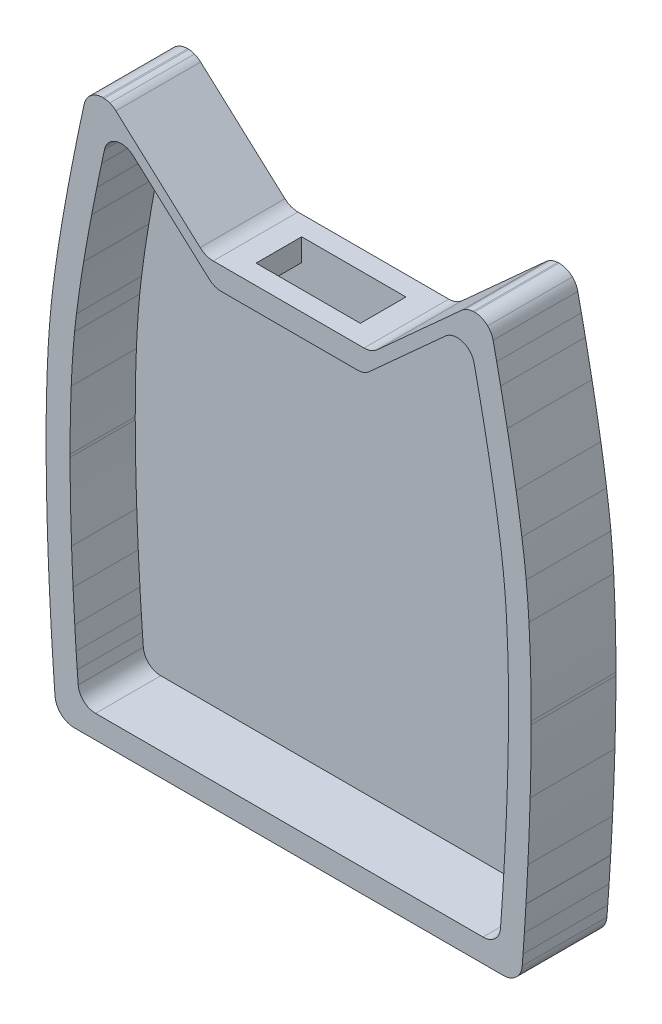
SolidWorks part; units mm, degrees
ref_plane "Front Plane" through (0, 0, 0) normal (0, 0, 1) x (1, 0, 0)
ref_plane "Top Plane" through (0, 0, 0) normal (0, 1, 0) x (1, 0, 0)
ref_plane "Right Plane" through (0, 0, 0) normal (1, 0, 0) x (0, 0, -1)
sketch "Sketch1" plane through (0, 0, 0) normal (0, 0, 1) x (1, 0, 0)
  line L0 (-74610.4504, -128792.8101) -> (-74623.3809, -128804.5097)
  line L1 (-74625.3861, -128805.2822) -> (-74648.5276, -128805.2822)
  line L2 (-74650.5328, -128804.5097) -> (-74663.4632, -128792.8101)
  line L3 (-74669.8394, -128877.9744) -> (-74604.0742, -128877.9744)
  arc A0 (-74625.3861, -128805.2822) -> (-74623.3809, -128804.5097) centre (-74625.3861, -128802.2936) ccw
  arc A1 (-74650.5328, -128804.5097) -> (-74648.5276, -128805.2822) centre (-74648.5276, -128802.2936) ccw
  arc A2 (-74663.4632, -128792.8101) -> (-74664.4011, -128792.2295) centre (-74665.4871, -128795.0316) ccw
  arc A3 (-74664.4011, -128792.2295) -> (-74665.2428, -128792.0421) centre (-74665.4489, -128794.9516) ccw
  arc A4 (-74665.2428, -128792.0421) -> (-74665.4521, -128792.0346) centre (-74665.452, -128794.9829) ccw
  arc A5 (-74665.4521, -128792.0346) -> (-74668.1554, -128793.8043) centre (-74665.4666, -128794.9621) ccw
  arc A6 (-74668.1554, -128793.8043) -> (-74668.3285, -128794.3514) centre (-74665.3558, -128794.991) ccw
  arc A7 (-74668.3285, -128794.3514) -> (-74668.8127, -128796.6154) centre (-74210.4972, -128893.4524) ccw
  arc A8 (-74668.8127, -128796.6154) -> (-74669.6285, -128800.5607) centre (-74215.6319, -128892.3844) ccw
  arc A9 (-74669.6285, -128800.5607) -> (-74670.5013, -128804.9966) centre (-74256.6242, -128884.1197) ccw
  arc A10 (-74670.5013, -128804.9966) -> (-74671.8625, -128812.5722) centre (-74344.668, -128867.4549) ccw
  arc A11 (-74671.8625, -128812.5722) -> (-74673.0862, -128820.8532) centre (-74471.6696, -128846.3871) ccw
  arc A12 (-74673.0862, -128820.8532) -> (-74673.4036, -128823.655) centre (-74549.975, -128836.2185) ccw
  arc A13 (-74673.4036, -128823.655) -> (-74673.9737, -128831.9341) centre (-74531.0189, -128837.6186) ccw
  arc A14 (-74673.9737, -128831.9341) -> (-74674.1705, -128842.0393) centre (-74433.1903, -128841.6785) ccw
  arc A15 (-74674.1705, -128842.0393) -> (-74674.1702, -128842.5188) centre (-74370.5267, -128842.0386) ccw
  arc A16 (-74674.1702, -128842.5188) -> (-74673.9133, -128855.4252) centre (-74296.3228, -128841.454) ccw
  arc A17 (-74673.9133, -128855.4252) -> (-74673.6609, -128861.373) centre (-74198.726, -128838.2406) ccw
  arc A18 (-74673.6609, -128861.373) -> (-74673.3731, -128866.7142) centre (-74161.6475, -128836.4629) ccw
  arc A19 (-74673.3731, -128866.7142) -> (-74673.1367, -128870.4811) centre (-74157.7529, -128836.253) ccw
  arc A20 (-74673.1367, -128870.4811) -> (-74672.9536, -128873.1301) centre (-74183.7854, -128837.9879) ccw
  arc A21 (-74672.9536, -128873.1301) -> (-74672.795, -128875.2658) centre (-74236.2197, -128841.7641) ccw
  arc A22 (-74672.795, -128875.2658) -> (-74669.8394, -128877.9744) centre (-74669.8639, -128875.0343) ccw
  arc A23 (-74604.0742, -128877.9744) -> (-74601.1186, -128875.2658) centre (-74604.0497, -128875.0343) ccw
  arc A24 (-74601.1186, -128875.2658) -> (-74600.9941, -128873.6003) centre (-75030.7638, -128842.2862) ccw
  arc A25 (-74600.9941, -128873.6003) -> (-74600.7912, -128870.6962) centre (-75084.5949, -128838.3701) ccw
  arc A26 (-74600.7912, -128870.6962) -> (-74600.5445, -128866.7814) centre (-75115.5828, -128836.2889) ccw
  arc A27 (-74600.5445, -128866.7814) -> (-74600.5406, -128866.7142) centre (-75116.7394, -128836.2135) ccw
  arc A28 (-74600.5406, -128866.7142) -> (-74600.2528, -128861.3729) centre (-75112.2699, -128836.4627) ccw
  arc A29 (-74600.2528, -128861.3729) -> (-74599.8985, -128852.287) centre (-75060.7265, -128838.8707) ccw
  arc A30 (-74599.8985, -128852.287) -> (-74599.7435, -128842.5188) centre (-74960.805, -128841.6735) ccw
  arc A31 (-74599.7435, -128842.5188) -> (-74599.7431, -128842.0393) centre (-74903.4023, -128842.0386) ccw
  arc A32 (-74599.7431, -128842.0393) -> (-74600.0837, -128829.0796) centre (-74823.121, -128841.4254) ccw
  arc A33 (-74600.0837, -128829.0796) -> (-74600.51, -128823.655) centre (-74730.0928, -128836.5682) ccw
  arc A34 (-74600.51, -128823.655) -> (-74601.1701, -128818.2711) centre (-74740.6628, -128838.1057) ccw
  arc A35 (-74601.1701, -128818.2711) -> (-74602.0512, -128812.5722) centre (-74824.1765, -128849.8308) ccw
  arc A36 (-74602.0512, -128812.5722) -> (-74603.4124, -128804.9967) centre (-74929.2472, -128867.4551) ccw
  arc A37 (-74603.4124, -128804.9967) -> (-74604.4266, -128799.864) centre (-75021.4303, -128884.9284) ccw
  arc A38 (-74604.4266, -128799.864) -> (-74605.0365, -128796.9208) centre (-75059.738, -128892.69) ccw
  arc A39 (-74605.0365, -128796.9208) -> (-74605.5852, -128794.3514) centre (-75063.9174, -128893.5596) ccw
  arc A40 (-74605.5852, -128794.3514) -> (-74606.4193, -128792.8477) centre (-74608.4315, -128794.9471) ccw
  arc A41 (-74606.4193, -128792.8477) -> (-74608.4615, -128792.0346) centre (-74608.4597, -128795.0013) ccw
  arc A42 (-74608.4615, -128792.0346) -> (-74608.6709, -128792.0421) centre (-74608.4616, -128794.9829) ccw
  arc A43 (-74608.6709, -128792.0421) -> (-74610.011, -128792.478) centre (-74608.464, -128794.9556) ccw
  arc A44 (-74610.011, -128792.478) -> (-74610.4504, -128792.8101) centre (-74608.3795, -128795.0941) ccw
  dimension "D1" = 72.6922
extrude "Boss-Extrude1" add sketch "Sketch1" along normal blind 13
sketch "Sketch2" plane through (0, 0, 13) normal (0, 0, 1) x (1, 0, 0)
  line B0 (-74612.8969, -128797.442) -> (-74624.5846, -128808.0172)
  line B1 (-74626.397, -128808.7154) -> (-74647.3143, -128808.7154)
  line B2 (-74649.1268, -128808.0172) -> (-74660.8144, -128797.442)
  line B3 (-74666.5778, -128874.4209) -> (-74607.1335, -128874.4209)
  arc B4 (-74626.397, -128808.7154) -> (-74624.5846, -128808.0172) centre (-74626.397, -128806.0141) ccw
  arc B5 (-74649.1268, -128808.0172) -> (-74647.3143, -128808.7154) centre (-74647.3143, -128806.014) ccw
  arc B6 (-74660.8144, -128797.442) -> (-74661.6621, -128796.9173) centre (-74662.6437, -128799.45) ccw
  arc B7 (-74661.6621, -128796.9173) -> (-74662.423, -128796.7479) centre (-74662.6092, -128799.3777) ccw
  arc B8 (-74662.423, -128796.7479) -> (-74662.6122, -128796.7411) centre (-74662.6121, -128799.406) ccw
  arc B9 (-74662.6122, -128796.7411) -> (-74665.0556, -128798.3408) centre (-74662.6252, -128799.3872) ccw
  arc B10 (-74665.0556, -128798.3408) -> (-74665.2121, -128798.8352) centre (-74662.5251, -128799.4134) ccw
  arc B11 (-74665.2121, -128798.8352) -> (-74665.6497, -128800.8816) centre (-74251.3845, -128888.4113) ccw
  arc B12 (-74665.6497, -128800.8816) -> (-74666.3872, -128804.4478) centre (-74256.0257, -128887.446) ccw
  arc B13 (-74666.3872, -128804.4478) -> (-74667.176, -128808.4573) centre (-74293.0781, -128879.9756) ccw
  arc B14 (-74667.176, -128808.4573) -> (-74668.4064, -128815.3047) centre (-74372.6597, -128864.9125) ccw
  arc B15 (-74668.4064, -128815.3047) -> (-74669.5125, -128822.7899) centre (-74487.4547, -128845.8696) ccw
  arc B16 (-74669.5125, -128822.7899) -> (-74669.7994, -128825.3223) centre (-74558.234, -128836.6783) ccw
  arc B17 (-74669.7994, -128825.3223) -> (-74670.3147, -128832.8057) centre (-74541.0998, -128837.9439) ccw
  arc B18 (-74670.3147, -128832.8057) -> (-74670.4926, -128841.9397) centre (-74452.6738, -128841.6136) ccw
  arc B19 (-74670.4926, -128841.9397) -> (-74670.4923, -128842.3731) centre (-74396.033, -128841.9391) ccw
  arc B20 (-74670.4923, -128842.3731) -> (-74670.2601, -128854.039) centre (-74328.9611, -128841.4106) ccw
  arc B21 (-74670.2601, -128854.039) -> (-74670.032, -128859.4151) centre (-74240.7447, -128838.5061) ccw
  arc B22 (-74670.032, -128859.4151) -> (-74669.7718, -128864.243) centre (-74207.2299, -128836.8993) ccw
  arc B23 (-74669.7718, -128864.243) -> (-74669.5582, -128867.6479) centre (-74203.7096, -128836.7095) ccw
  arc B24 (-74669.5582, -128867.6479) -> (-74669.3927, -128870.0422) centre (-74227.2401, -128838.2777) ccw
  arc B25 (-74669.3927, -128870.0422) -> (-74669.2493, -128871.9726) centre (-74274.6347, -128841.691) ccw
  arc B26 (-74669.2493, -128871.9726) -> (-74666.5778, -128874.4209) centre (-74666.5999, -128871.7634) ccw
  arc B27 (-74607.1335, -128874.4209) -> (-74604.462, -128871.9726) centre (-74607.1114, -128871.7634) ccw
  arc B28 (-74604.462, -128871.9726) -> (-74604.3494, -128870.4673) centre (-74992.8125, -128842.1629) ccw
  arc B29 (-74604.3494, -128870.4673) -> (-74604.1661, -128867.8423) centre (-75041.4697, -128838.6231) ccw
  arc B30 (-74604.1661, -128867.8423) -> (-74603.9431, -128864.3037) centre (-75069.4793, -128836.7419) ccw
  arc B31 (-74603.9431, -128864.3037) -> (-74603.9395, -128864.243) centre (-75070.5247, -128836.674) ccw
  arc B32 (-74603.9395, -128864.243) -> (-74603.6793, -128859.4151) centre (-75066.4848, -128836.8991) ccw
  arc B33 (-74603.6793, -128859.4151) -> (-74603.3592, -128851.2025) centre (-75019.8954, -128839.0756) ccw
  arc B34 (-74603.3592, -128851.2025) -> (-74603.219, -128842.3731) centre (-74929.5777, -128841.609) ccw
  arc B35 (-74603.219, -128842.3731) -> (-74603.2187, -128841.9397) centre (-74877.6921, -128841.9391) ccw
  arc B36 (-74603.2187, -128841.9397) -> (-74603.5265, -128830.2256) centre (-74805.1269, -128841.3848) ccw
  arc B37 (-74603.5265, -128830.2256) -> (-74603.9119, -128825.3223) centre (-74721.04, -128836.9945) ccw
  arc B38 (-74603.9119, -128825.3223) -> (-74604.5085, -128820.4559) centre (-74730.5941, -128838.3841) ccw
  arc B39 (-74604.5085, -128820.4559) -> (-74605.3049, -128815.3047) centre (-74806.081, -128848.9823) ccw
  arc B40 (-74605.3049, -128815.3047) -> (-74606.5353, -128808.4574) centre (-74901.053, -128864.9127) ccw
  arc B41 (-74606.5353, -128808.4574) -> (-74607.452, -128803.818) centre (-74984.3761, -128880.7066) ccw
  arc B42 (-74607.452, -128803.818) -> (-74608.0033, -128801.1577) centre (-75019.0019, -128887.7221) ccw
  arc B43 (-74608.0033, -128801.1577) -> (-74608.4992, -128798.8352) centre (-75022.7796, -128888.5082) ccw
  arc B44 (-74608.4992, -128798.8352) -> (-74609.2532, -128797.4761) centre (-74611.072, -128799.3737) ccw
  arc B45 (-74609.2532, -128797.4761) -> (-74611.0991, -128796.7411) centre (-74611.0975, -128799.4227) ccw
  arc B46 (-74611.0991, -128796.7411) -> (-74611.2883, -128796.7479) centre (-74611.0992, -128799.406) ccw
  arc B47 (-74611.2883, -128796.7479) -> (-74612.4996, -128797.1419) centre (-74611.1014, -128799.3814) ccw
  arc B48 (-74612.4996, -128797.1419) -> (-74612.8969, -128797.442) centre (-74611.025, -128799.5065) ccw
sketch_block_instance "Block1-1"
sketch_block "Block1"
extrude "Cut-Extrude1" cut sketch "Sketch2" against normal blind 10
sketch "Sketch3" plane through (0, -128805.2822, 0) normal (0, 1, 0) x (1, 0, 0)
  line L0 (-74625.3861, 0) -> (-74648.5276, 0) construction
  line L1 (-74644.9561, -3) -> (-74628.9561, -3)
  line L2 (-74644.9561, -3) -> (-74644.9561, -10)
  line L3 (-74644.9561, -10) -> (-74628.9561, -10)
  line L4 (-74628.9561, -3) -> (-74628.9561, -10)
  line L6 (-74625.3861, -13) -> (-74625.3861, 0) construction
  dimension "D1" = 16
  dimension "D2" = 7
  dimension "D3" = 3
  dimension "D4" = 3.57
extrude "Cut-Extrude2" cut sketch "Sketch3" against normal blind 10
